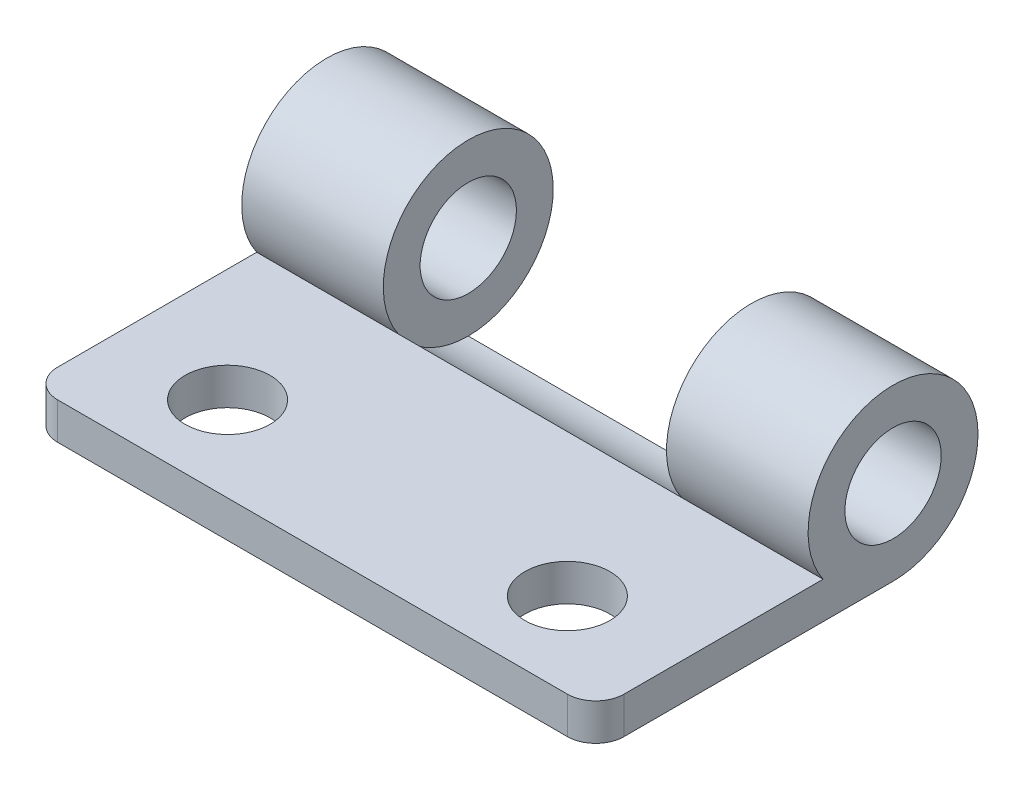
SolidWorks part; units mm, degrees
ref_plane "前视基准面" through (0, 0, 0) normal (0, 0, 1) x (1, 0, 0)
ref_plane "上视基准面" through (0, 0, 0) normal (0, 1, 0) x (1, 0, 0)
ref_plane "右视基准面" through (0, 0, 0) normal (1, 0, 0) x (0, 0, -1)
sketch "草图1" plane through (0, 0, 0) normal (1, 0, 0) x (0, 0, -1)
  line L1 (0, 0) -> (10.5, 0)
  line L2 (0, 0) -> (0, 1.3)
  line L3 (0, 1.3) -> (10.5, 1.3)
  line L4 (10.5, 0) -> (10.5, 1.3)
extrude "凸台-拉伸2" add sketch "草图1" along normal blind 20
sketch "草图2" plane through (20, 0, 0) normal (1, 0, 0) x (0, 0, -1)
  circle A0 centre (10.5, 3) radius 3
  circle A1 centre (10.5, 3) radius 1.7
extrude "凸台-拉伸3" add sketch "草图2" against normal blind 5
sketch "草图3" plane through (15, 0, 0) normal (-1, 0, 0) x (0, 0, 1)
  circle A0 centre (-10.5, 3) radius 3
extrude "切除-拉伸1" cut sketch "草图3" along normal blind 10
ref_plane "基准面1" through (10, 0, 0) normal (-1, 0, 0) x (0, 0, 1)
mirror "镜向1" about plane through (10, 0, 0) normal (-1, 0, 0) of "凸台-拉伸3"
sketch "草图4" plane through (0, 1.3, 0) normal (0, 1, 0) x (1, 0, 0)
  line L0 (20, 0) -> (0, 0) construction
  line L2 (0, 8.0282) -> (0, 0) construction
  circle A0 centre (4, 3) radius 1.5
  dimension "D1" = 3
  dimension "D2" = 4
extrude "切除-拉伸2" cut sketch "草图4" against normal blind 10
mirror "镜向2" about plane through (10, 0, 0) normal (-1, 0, 0) of "切除-拉伸2"
fillet "圆角1" radius 1 2 edges at (20, 0.65, 0) (0, 0.65, 0)
